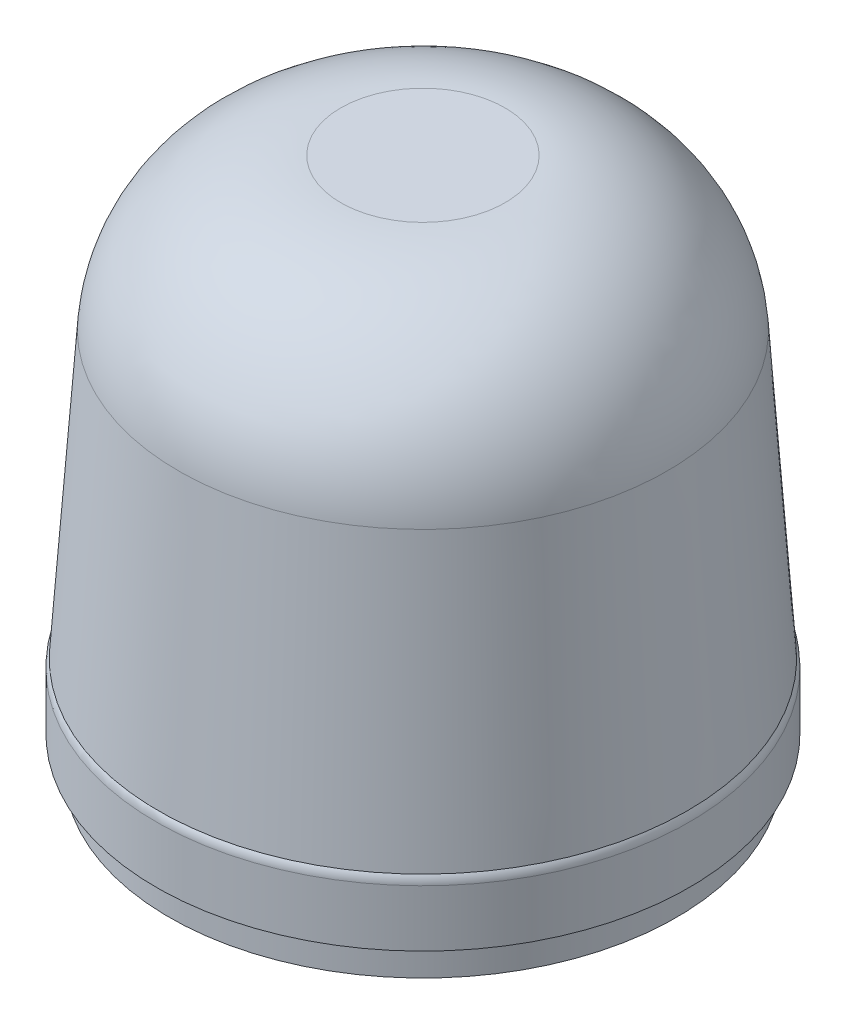
SolidWorks part; units mm, degrees
ref_plane "Alzado" through (0, 0, 0) normal (0, 0, 1) x (1, 0, 0)
ref_plane "Planta" through (0, 0, 0) normal (0, 1, 0) x (1, 0, 0)
ref_plane "Vista lateral" through (0, 0, 0) normal (1, 0, 0) x (0, 0, -1)
sketch "Sketch1" plane through (0, 0, 0) normal (0, 0, 1) x (1, 0, 0)
  line L0 (0, 0) -> (-78, 0)
  line L1 (-78, 0) -> (-78, 8)
  line L2 (-78, 8) -> (-82, 10)
  line L3 (-82, 10) -> (-82, 27.409)
  line L4 (-81.2763, 30) -> (-75.1586, 117.4878)
  line L5 (-25.2804, 164) -> (0, 164)
  line L6 (0, 164) -> (0, 0) construction
  line L7 (0, 0) -> (0, 164)
  arc A0 (-82, 27.409) -> (-81.2763, 30) centre (-77, 27.409) cw
  arc A1 (-75.1586, 117.4878) -> (-25.2804, 164) centre (-25.2804, 114) cw
  dimension "D4" = 50
  dimension "D5" = 5
  dimension "D1" = 156
  dimension "D2" = 164
  dimension "D3" = 164
  dimension "D6" = 20
  dimension "D7" = 8
  dimension "D8" = 10
  dimension "D9" = 4
  dimension "D10" = 27.409
revolve "Revolve1" add sketch "Sketch1" angle 360 about L6
sketch "Sketch3" plane through (0, 0, 0) normal (1, 0, 0) x (0, 0, -1)
  line L0 (-80.955, 129.0722) -> (-80.955, 64.7175) construction
  arc A0 (-5.5686, 22.9437) -> (-5.5686, 141.5111) centre (-90.2785, 82.2274) ccw
  arc A1 (-5.5686, 22.9437) -> (-5.5686, 141.5111) centre (-80.955, 82.2274) ccw
revolve "Cut-Revolve1" [suppressed] cut sketch "Sketch3" angle 80 mid plane about L0
sketch "Sketch4" plane through (0, 0, 0) normal (0, -1, 0) x (1, 0, 0)
  line L0 (0, 0) -> (-26.8701, 26.8701)
  line L1 (50, 0) -> (-50, 0) construction
  line L2 (0, 0) -> (64.7527, -5.6651)
  circle A0 centre (0, 0) radius 38
  circle A1 centre (0, 0) radius 65
  dimension "D1" = 76
  dimension "D2" = 45
  dimension "D3" = 130
  dimension "D4" = 5
hole_wizard "Ø4.0 (4) Diameter Hole1" positions "Sketch6" profile "Sketch5" hole size "Ø4.0" standard "ANSI Metric"
sketch "Sketch6" plane through (0, 0, 0) normal (0, -1, 0) x (-1, 0, 0)
  point P0 (26.8701, -26.8701)
sketch "Sketch5" plane through (-26.8701, 0, 26.8701) normal (1, 0, 0) x (0, 0, -1)
  line L0 (0, 0) -> (0, 20.2017)
  line L1 (0, 20.2017) -> (2, 19)
  line L2 (2, 19) -> (2, 0)
  line L5 (2, 0) -> (0, 0)
  line L10 (0, 20.2017) -> (-2, 19) construction
  line L11 (0, -6.35) -> (0, 107.95) construction
  dimension "Hole Dia." = 4
  dimension "Hole Depth" = 19
  dimension "Drill Angle" = 118
pattern_circular "CirPattern1" count 4 every 90 about axis through (0, 0, 0) along (0, 1, 0) of "Ø4.0 (4) Diameter Hole1"
hole_wizard "Ø5.0 (5) Diameter Hole1" positions "Sketch8" profile "Sketch7" hole size "Ø5.0" standard "ANSI Metric"
sketch "Sketch8" plane through (0, 0, 0) normal (0, -1, 0) x (-1, 0, 0)
  point P0 (-64.7527, 5.6651)
sketch "Sketch7" plane through (64.7527, 0, -5.6651) normal (1, 0, 0) x (0, 0, -1)
  line L0 (0, 0) -> (0, 20.5022)
  line L1 (0, 20.5022) -> (2.5, 19)
  line L2 (2.5, 19) -> (2.5, 0)
  line L5 (2.5, 0) -> (0, 0)
  line L10 (0, 20.5022) -> (-2.5, 19) construction
  line L11 (0, -6.35) -> (0, 107.95) construction
  dimension "Hole Dia." = 5
  dimension "Hole Depth" = 19
  dimension "Drill Angle" = 118
pattern_circular "CirPattern2" count 3 over 360 about axis through (0, 0, 0) along (0, 1, 0) of "Ø5.0 (5) Diameter Hole1"
scale "Scale1" [suppressed]
scale "Scale2" scale about centroid uniform scaling yes scale factor 0.5
scale "Scale3" scale about centroid uniform scaling yes scale factor 0.5
